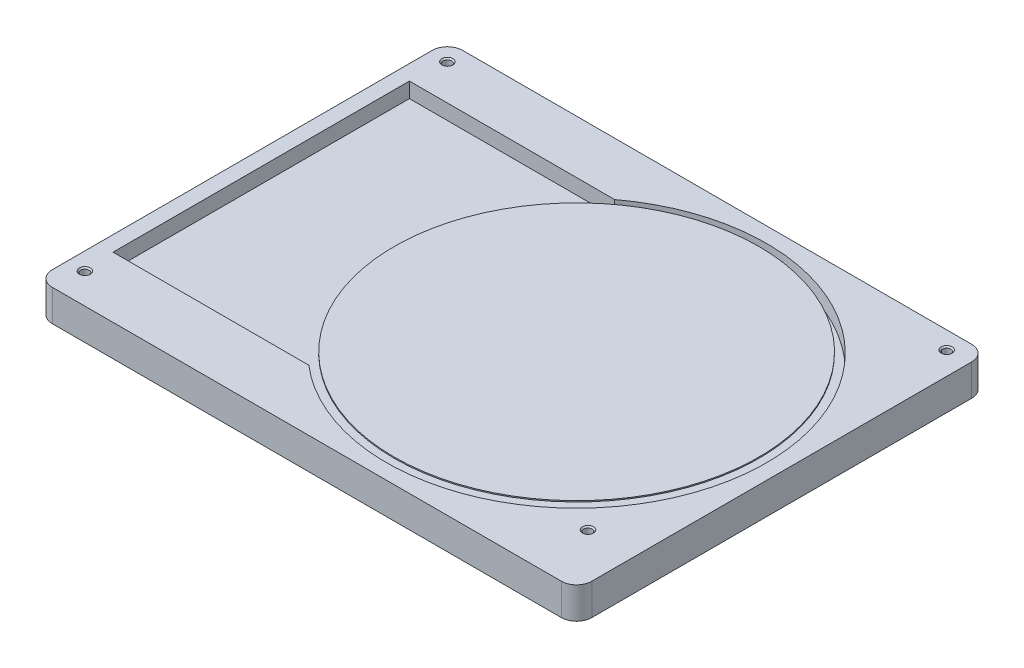
SolidWorks part; units mm, degrees
material "6061-T6 (SS)"
ref_plane "Front Plane" through (0, 0, 0) normal (0, 0, 1) x (1, 0, 0)
ref_plane "Top Plane" through (0, 0, 0) normal (0, 1, 0) x (1, 0, 0)
ref_plane "Right Plane" through (0, 0, 0) normal (1, 0, 0) x (0, 0, -1)
sketch "Sketch1" plane through (0, 0, 0) normal (0, 1, 0) x (1, 0, 0)
  line L1 (-35.5, -27) -> (35.5, -27)
  line L2 (-35.5, -27) -> (-35.5, 27)
  line L3 (-35.5, 27) -> (35.5, 27)
  line L4 (35.5, -27) -> (35.5, 27)
  line L5 (-35.5, -27) -> (35.5, 27) construction
  line L6 (-35.5, 27) -> (35.5, -27) construction
  point P0 (0, 0)
  dimension "D1" = 71
  dimension "D2" = 54
extrude "Boss-Extrude1" add sketch "Sketch1" along normal blind 4.15
sketch "Sketch2" plane through (0, 0, 0) normal (0, -1, 0) x (1, 0, 0)
  line L0 (-35.5, -27) -> (-35.5, 27) construction
  line L1 (-32.5, -7) -> (-32.5, -24)
  line L2 (-32.5, -24) -> (-15.5, -24)
  line L3 (-15.5, -24) -> (-15.5, -19)
  line L4 (-32.5, -7) -> (-27.5, -7)
  line L5 (35.5, -27) -> (-35.5, -27) construction
  circle A0 centre (8.5, 0) radius 11
  arc A1 (-27.5, -7) -> (-15.5, -19) centre (-27.5, -19) cw
  dimension "D1" = 22
  dimension "D7" = 12
  dimension "D2" = 44
  dimension "D3" = 3
  dimension "D4" = 3
  dimension "D5" = 20
  dimension "D6" = 20
extrude "Boss-Extrude2" [suppressed] add sketch "Sketch2" along normal blind 1
sketch "Sketch3" plane through (0, 4.15, 0) normal (0, 1, 0) x (1, 0, 0)
  line L0 (-35.5, 27) -> (-35.5, -27) construction
  line L1 (-35.5, -27) -> (35.5, -27) construction
  line L2 (-6.5, 20) -> (-33.5, 20)
  line L4 (-7.7481, -19) -> (-33.5, -19)
  line L5 (-33.5, 20) -> (-33.5, -19)
  line L6 (35.5, 27) -> (-35.5, 27) construction
  arc A0 (-7.7481, -19) -> (-6.5, 20) centre (8.5, 0) ccw
  dimension "D2" = 50
  dimension "D1" = 44
  dimension "D3" = 2
  dimension "D4" = 8
  dimension "D5" = 7
extrude "Cut-Extrude1" cut sketch "Sketch3" against normal blind 2
sketch "Sketch4" plane through (0, 2.15, 0) normal (0, 1, 0) x (1, 0, 0)
  line L0 (-35.5, 27) -> (-35.5, -27) construction
  circle A0 centre (8.5, 0) radius 7.5
  dimension "D2" = 15
  dimension "D1" = 44
extrude "Boss-Extrude3" add sketch "Sketch4" along normal blind 2
sketch "Sketch5" plane through (0, 4.15, 0) normal (0, 1, 0) x (1, 0, 0)
  line L0 (-35.5, 27) -> (-35.5, -27) construction
  circle A0 centre (8.5, 0) radius 24
  dimension "D2" = 48
  dimension "D1" = 44
extrude "Boss-Extrude4" add sketch "Sketch5" along normal blind 0.15
sketch "Sketch6" plane through (0, 4.3, 0) normal (0, 1, 0) x (1, 0, 0)
  line L0 (-35.5, 27) -> (-35.5, -27) construction
  circle A0 centre (8.5, 0) radius 7
  dimension "D2" = 14
  dimension "D1" = 44
extrude "Boss-Extrude5" [suppressed] add sketch "Sketch6" along normal blind 0.75
hole_wizard "M1.4x0.3 Tapped Hole1" positions "Sketch7" profile "Sketch8" tap size "M1.4x0.3" standard "ANSI Metric" end condition through all
sketch "Sketch7" plane through (0, 4.15, 0) normal (0, 1, 0) x (1, 0, 0)
  line L0 (35.5, -27) -> (35.5, 27) construction
  line L1 (35.5, 27) -> (-35.5, 27) construction
  line L2 (-35.5, 27) -> (-35.5, -27) construction
  line L3 (-35.5, -27) -> (35.5, -27) construction
  point P0 (-33.2, 24.7)
  point P3 (-33.2, -23)
  point P5 (29.4, -19.4)
  point P7 (32.5, 24.7)
  dimension "D1" = 3
  dimension "D2" = 2.3
  dimension "D3" = 2.3
  dimension "D4" = 2.3
  dimension "D5" = 4
  dimension "D6" = 2.3
  dimension "D7" = 7.6
  dimension "D8" = 6.1
sketch "Sketch8" plane through (-33.2, 4.15, -24.7) normal (1, 0, 0) x (0, 0, 1)
  line L0 (0, 0) -> (0, 4.15)
  line L1 (0, 4.15) -> (0.55, 4.15)
  line L2 (0.55, 4.15) -> (0.55, 0.175)
  line L3 (0.55, 0.175) -> (0.725, 0)
  line L5 (0.725, 0) -> (0, 0)
  line L6 (-0.55, 0.175) -> (-0.725, 0) construction
  line L11 (0, -6.35) -> (0, 107.95) construction
  dimension "Thru Tap Drill Dia." = 1.1
  dimension "Thru Tap Drill Depth" = 4.15
  dimension "Near C'Sink Dia." = 1.45
  dimension "Near C'Sink Angle" = 90
cosmetic thread "Hole Thread1" parameters "D2"=1.4
cosmetic thread "Hole Thread2" parameters "D2"=1.4
cosmetic thread "Hole Thread3" parameters "D2"=1.4
cosmetic thread "Hole Thread4" parameters "D2"=1.4
fillet "Fillet1" radius 2 4 edges at (-35.5, 2.075, 27) (-35.5, 2.075, -27) (35.5, 2.075, -27) (35.5, 2.075, 27)
fillet "Fillet2" [suppressed] radius 1
fillet "Fillet3" [suppressed] radius 1
